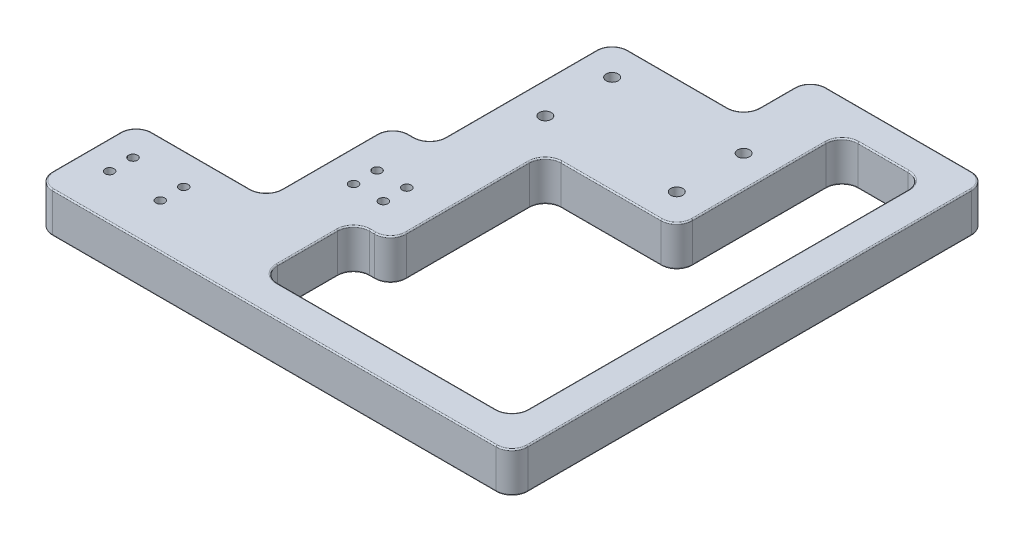
SolidWorks part; units mm, degrees
other "Markup1"
sketch "Sketch12" plane through (370, 12.7, 0) normal (0.2218, 0.7641, 0.6058) x (0.9744, -0.1978, -0.1071)
material "Delrin 2700 NC010, Low Viscosity Acetal Copolymer (SS)"
ref_plane "Front Plane" through (0, 0, 0) normal (0, 0, 1) x (1, 0, 0)
ref_plane "Top Plane" through (0, 0, 0) normal (0, 1, 0) x (1, 0, 0)
ref_plane "Right Plane" through (0, 0, 0) normal (1, 0, 0) x (0, 0, -1)
sketch "Sketch1" plane through (0, 0, 0) normal (0, 1, 0) x (1, 0, 0)
  line L1 (0, 0) -> (150, 0)
  line L2 (0, 0) -> (0, 150)
  line L3 (0, 150) -> (150, 150)
  line L4 (150, 0) -> (150, 150)
  dimension "D1" = 150
  dimension "D2" = 150
extrude "Boss-Extrude1" add sketch "Sketch1" along normal blind 12.7
hole_wizard "M3 Clearance Hole1" positions "Sketch2" profile "Sketch3" hole size "M3" standard "ISO" end condition through all
sketch "Sketch2" plane through (0, 12.7, 0) normal (0, 1, 0) x (1, 0, 0)
  point P0 (9, 21.4)
  point P3 (25, 21.4)
  point P6 (25, 14)
  point P9 (9, 14)
  point P12 (51, 56.4)
  point P15 (60.4, 56.4)
  point P18 (60.4, 49)
  point P21 (51, 49)
sketch "Sketch3" plane through (9, 12.7, -21.4) normal (1, 0, 0) x (0, 0, 1)
  line L0 (0, 0) -> (0, 12.7)
  line L1 (0, 12.7) -> (1.4, 12.7)
  line L2 (1.4, 12.7) -> (1.4, 0)
  line L5 (1.4, 0) -> (0, 0)
  line L11 (0, -6.35) -> (0, 107.95) construction
  dimension "Thru Hole Dia." = 2.8
  dimension "Thru Hole Depth" = 12.7
hole_wizard "M4 Clearance Hole1" positions "Sketch6" profile "Sketch7" hole size "M4" standard "ISO" end condition through all
sketch "Sketch6" plane through (0, 12.7, 0) normal (0, 1, 0) x (1, 0, 0)
  point P0 (62.65, 97.8493)
  point P3 (62.65, 118.9493)
  point P6 (104.15, 118.9493)
  point P9 (104.15, 97.8493)
sketch "Sketch7" plane through (62.65, 12.7, -97.8493) normal (1, 0, 0) x (0, 0, 1)
  line L0 (0, 0) -> (0, 12.7)
  line L1 (0, 12.7) -> (1.9, 12.7)
  line L2 (1.9, 12.7) -> (1.9, 0)
  line L5 (1.9, 0) -> (0, 0)
  line L11 (0, -6.35) -> (0, 107.95) construction
  dimension "Thru Hole Dia." = 3.8
  dimension "Thru Hole Depth" = 12.7
sketch "Sketch14" plane through (0, 12.7, 0) normal (0, 1, 0) x (1, 0, 0)
  line L0 (150, 0) -> (150, 150) construction
  line L1 (72.65, 87.8493) -> (140, 87.8493)
  line L2 (72.65, 87.8493) -> (72.65, 10)
  line L3 (72.65, 10) -> (140, 10)
  line L4 (140, 87.8493) -> (140, 10)
  line L5 (0, 150) -> (52.65, 150)
  line L6 (0, 150) -> (0, 71.4)
  line L7 (0, 71.4) -> (52.65, 71.4)
  line L8 (52.65, 150) -> (52.65, 71.4)
  line L9 (0, 0) -> (150, 0) construction
  line L10 (150, 150) -> (0, 150) construction
  line L12 (0, 150) -> (0, 0) construction
  line L13 (0, 71.4) -> (41, 71.4)
  line L14 (0, 71.4) -> (0, 31.4)
  line L15 (0, 31.4) -> (41, 31.4)
  line L16 (41, 71.4) -> (41, 31.4)
  line L17 (140, 87.8493) -> (114.15, 87.8493)
  line L18 (140, 87.8493) -> (140, 140)
  line L19 (140, 140) -> (114.15, 140)
  line L20 (114.15, 87.8493) -> (114.15, 140)
  line L21 (72.65, 10) -> (61, 10)
  line L22 (72.65, 10) -> (72.65, 39)
  line L23 (72.65, 39) -> (61, 39)
  line L24 (61, 10) -> (61, 39)
  line L26 (52.65, 150) -> (94.15, 150)
  line L27 (52.65, 150) -> (52.65, 128.9493)
  line L28 (52.65, 128.9493) -> (94.15, 128.9493)
  line L29 (94.15, 150) -> (94.15, 128.9493)
  circle A1 centre (104.15, 97.8493) radius 1.9 construction
  circle A2 centre (51, 56.4) radius 1.4 construction
  circle A3 centre (62.65, 118.9493) radius 1.9 construction
  circle A4 centre (25, 21.4) radius 1.4 construction
  circle A5 centre (104.15, 118.9493) radius 1.9 construction
  circle A6 centre (60.4, 49) radius 1.4 construction
  line M24 (150, 150) -> (0, 150)
  dimension "D10" = 10
  dimension "D1" = 10
  dimension "D2" = 10
  dimension "D3" = 20
  dimension "D4" = 10
  dimension "D5" = 0
  dimension "D6" = 0
  dimension "D7" = 15
  dimension "D8" = 10
  dimension "D9" = 10
  dimension "D11" = 10
  dimension "D12" = 10
  dimension "D13" = 10
  dimension "D14" = 20
  dimension "D15" = 10
  dimension "D16" = 20
extrude "Cut-Extrude1" cut sketch "Sketch14" against normal through all both and the other way through all contours L8 L5 L6 L7 | L16 L7 L14 L15 | L4 L1 L2 L3 | L20 L1 L18 L19 | L29 L8 L28 M24 | L24 L21 L2 L23
fillet "Fillet1" radius 5 18 edges at (150, 6.35, -150) (150, 6.35, 0) (0, 6.35, 0) (52.65, 6.35, -71.4) (140, 6.35, -10) (72.65, 6.35, -87.8493) (140, 6.35, -140) (114.15, 6.35, -140) (114.15, 6.35, -87.8493) (41, 6.35, -31.4) (41, 6.35, -71.4) (94.15, 6.35, -150) (94.15, 6.35, -128.9493) (52.65, 6.35, -128.9493) (0, 6.35, -31.4) (61, 6.35, -10) (72.65, 6.35, -39) (61, 6.35, -39)
fillet "Fillet2" radius 0.4 72 edges at (1.4645, 0, -1.4645) (0, 0, -15.7) (122.075, 0, -150) (148.5355, 0, -148.5355) (150, 0, -75) (148.5355, 0, -1.4645) (1.4645, 12.7, -1.4645) (0, 12.7, -15.7) (122.075, 12.7, -150) (148.5355, 12.7, -148.5355) (150, 12.7, -75) (148.5355, 12.7, -1.4645) (75, 0, 0) (75, 12.7, 0) (138.5355, 0, -11.4645) (100.5, 0, -10) (72.65, 0, -63.4246) (74.1145, 0, -86.3848) (93.4, 0, -87.8493) (51.1855, 0, -72.8645) (46.825, 0, -71.4) (46.825, 12.7, -71.4) (51.1855, 12.7, -72.8645) (52.65, 12.7, -100.1746) (100.5, 12.7, -10) (138.5355, 12.7, -11.4645) (140, 12.7, -75) (93.4, 12.7, -87.8493) (74.1145, 12.7, -86.3848) (140, 0, -75) (52.65, 0, -100.1746) (72.65, 12.7, -63.4246) (138.5355, 0, -138.5355) (127.075, 0, -140) (115.6145, 0, -138.5355) (114.15, 0, -113.9246) (112.6855, 0, -89.3137) (20.5, 0, -31.4) (39.5355, 0, -32.8645) (41, 0, -51.4) (42.4645, 0, -69.9355) (20.5, 12.7, -31.4) (39.5355, 12.7, -32.8645) (41, 12.7, -51.4) (42.4645, 12.7, -69.9355) (138.5355, 12.7, -138.5355) (127.075, 12.7, -140) (115.6145, 12.7, -138.5355) (114.15, 12.7, -113.9246) (112.6855, 12.7, -89.3137) (1.4645, 0, -29.9355) (54.1145, 0, -127.4848) (73.4, 0, -128.9493) (92.6855, 0, -130.4137) (94.15, 0, -139.4746) (95.6145, 0, -148.5355) (1.4645, 12.7, -29.9355) (54.1145, 12.7, -127.4848) (73.4, 12.7, -128.9493) (92.6855, 12.7, -130.4137) (94.15, 12.7, -139.4746) (95.6145, 12.7, -148.5355) (71.1855, 0, -40.4645) (66.825, 0, -39) (62.4645, 0, -37.5355) (61, 0, -24.5) (62.4645, 0, -11.4645) (71.1855, 12.7, -40.4645) (66.825, 12.7, -39) (62.4645, 12.7, -37.5355) (61, 12.7, -24.5) (62.4645, 12.7, -11.4645)
